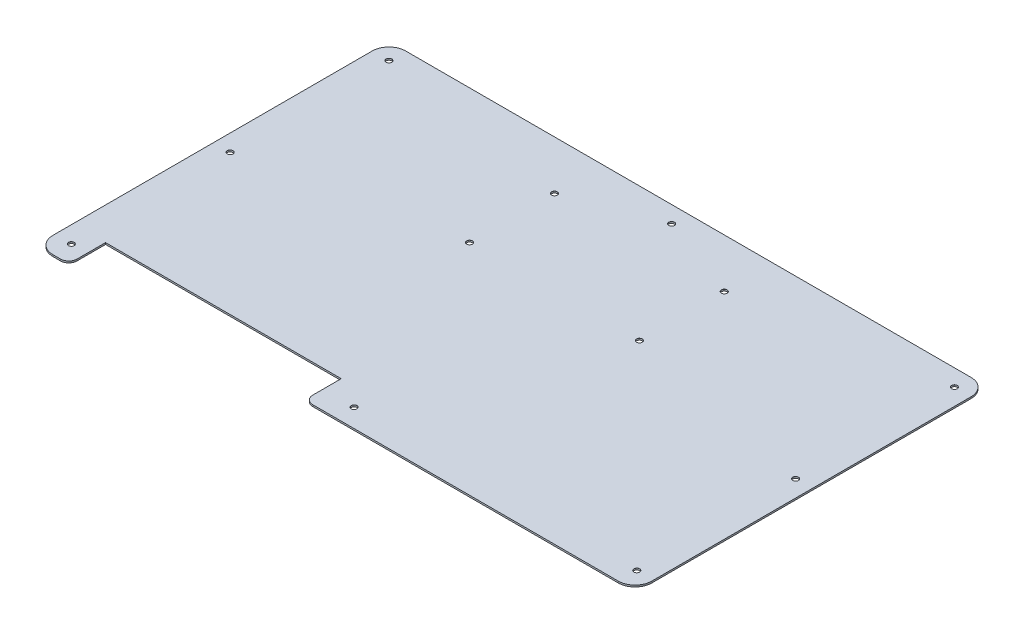
SolidWorks part; units mm, degrees
ref_plane "Front Plane" through (0, 0, 0) normal (0, 0, 1) x (1, 0, 0)
ref_plane "Top Plane" through (0, 0, 0) normal (0, 1, 0) x (1, 0, 0)
ref_plane "Right Plane" through (0, 0, 0) normal (1, 0, 0) x (0, 0, -1)
sketch "Sketch1" plane through (0, 0, 0) normal (0, 1, 0) x (1, 0, 0)
  line L0 (-159.635, -105.525) -> (-159.635, -83.525)
  line L1 (-179.135, 105.525) -> (179.135, 105.525)
  line L2 (-179.135, 105.525) -> (-179.135, -105.525)
  line L3 (-179.135, -105.525) -> (-159.635, -105.525)
  line L4 (179.135, 105.525) -> (179.135, -105.525)
  line L5 (-179.135, 105.525) -> (179.135, -105.525) construction
  line L6 (-179.135, -105.525) -> (179.135, 105.525) construction
  line L7 (-159.635, -83.525) -> (-18.635, -83.525)
  line L8 (-18.635, -83.525) -> (-18.635, -105.525)
  line L9 (-18.635, -105.525) -> (179.135, -105.525)
  point P0 (0, 0)
  dimension "D1" = 358.27
  dimension "D2" = 211.05
  dimension "D3" = 22
  dimension "D4" = 19.5
  dimension "D5" = 141
extrude "Boss-Extrude1" add sketch "Sketch1" along normal blind 1
fillet "Fillet1" radius 10 4 edges at (-179.135, 0.5, -105.525) (-179.135, 0.5, 105.525) (179.135, 0.5, -105.525) (179.135, 0.5, 105.525)
hole_wizard "M3 Clearance Hole1" positions "Sketch2" profile "Sketch3" hole size "M3" standard "ANSI Metric" end condition through all
sketch "Sketch2" plane through (0, 1, 0) normal (0, 1, 0) x (1, 0, 0)
  point P0 (169.135, 0.525)
  point P3 (169.135, -94.475)
  point P6 (169.135, 95.525)
  point P9 (0, 95.525)
  point P12 (-169.135, 95.525)
  point P15 (-169.135, 0.525)
  point P18 (-169.135, -94.475)
  point P21 (0, -94.475)
sketch "Sketch3" plane through (169.135, 1, -0.525) normal (1, 0, 0) x (0, 0, 1)
  line L0 (0, 0) -> (0, 1)
  line L1 (0, 1) -> (1.7, 1)
  line L2 (1.7, 1) -> (1.7, 0.025)
  line L3 (1.7, 0.025) -> (1.725, 0)
  line L5 (1.725, 0) -> (0, 0)
  line L6 (-1.7, 0.025) -> (-1.725, 0) construction
  line L11 (0, -6.35) -> (0, 107.95) construction
  dimension "Thru Hole Dia." = 3.4
  dimension "Thru Hole Depth" = 1
  dimension "Near C'Sink Dia." = 3.45
  dimension "Near C'Sink Angle" = 90
hole_wizard "M3 Clearance Hole3" positions "Sketch4" profile "Sketch5" hole size "M3" standard "ANSI Metric" end condition through all
sketch "Sketch4" plane through (0, 1, 0) normal (0, 1, 0) x (1, 0, 0)
  line L0 (0, 0) -> (0, 50.8) construction
  line L3 (-50.8, 25.4) -> (50.8, 25.4)
  line L4 (-50.8, 25.4) -> (-50.8, 76.2)
  line L5 (-50.8, 76.2) -> (50.8, 76.2)
  line L6 (50.8, 25.4) -> (50.8, 76.2)
  line L7 (-50.8, 25.4) -> (50.8, 76.2) construction
  line L8 (-50.8, 76.2) -> (50.8, 25.4) construction
  point P7 (50.8, 76.2)
  point P106 (-50.8, 25.4)
  point P107 (-50.8, 76.2)
  point P108 (50.8, 25.4)
  dimension "D1" = 50.8
  dimension "D2" = 101.6
  dimension "D3" = 50.8
sketch "Sketch5" plane through (50.8, 1, -25.4) normal (1, 0, 0) x (0, 0, 1)
  line L0 (0, 0) -> (0, 1)
  line L1 (0, 1) -> (1.7, 1)
  line L2 (1.7, 1) -> (1.7, 0.025)
  line L3 (1.7, 0.025) -> (1.725, 0)
  line L5 (1.725, 0) -> (0, 0)
  line L6 (-1.7, 0.025) -> (-1.725, 0) construction
  line L11 (0, -6.35) -> (0, 107.95) construction
  dimension "Thru Hole Dia." = 3.4
  dimension "Thru Hole Depth" = 1
  dimension "Near C'Sink Dia." = 3.45
  dimension "Near C'Sink Angle" = 90
fillet "Fillet2" radius 5 2 edges at (-18.635, 0.5, 105.525) (-159.635, 0.5, 105.525)
